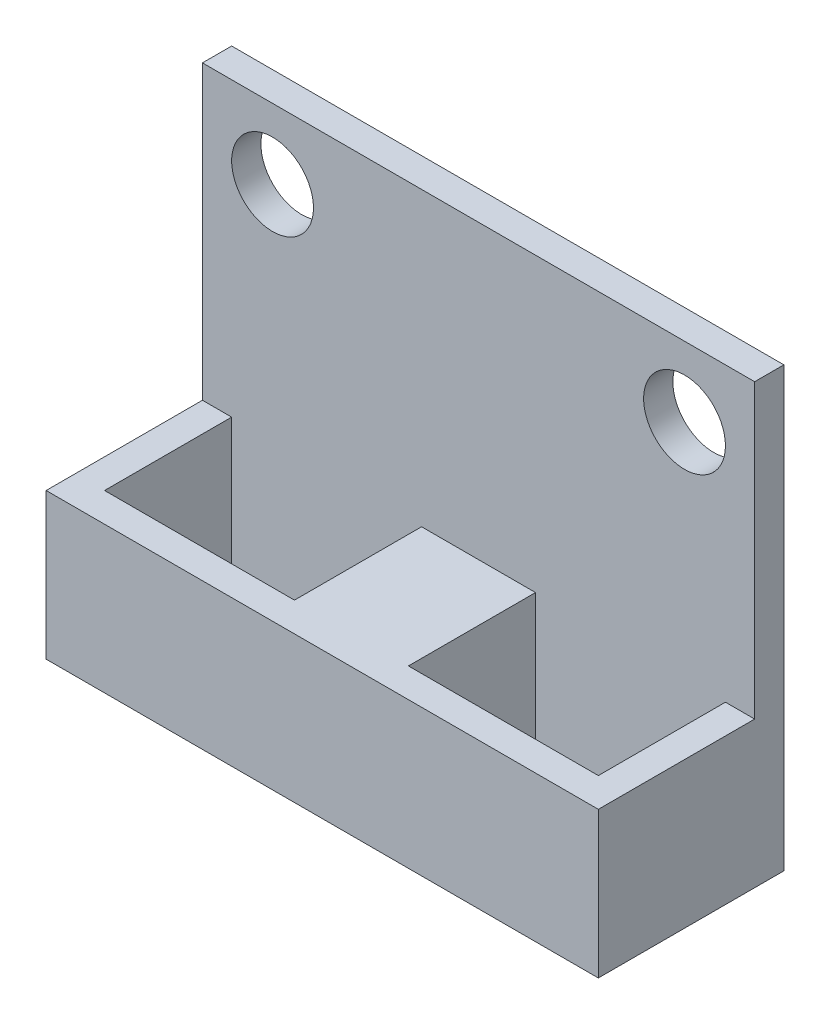
SolidWorks part; units mm, degrees
ref_plane "Front Plane" through (0, 0, 0) normal (0, 0, 1) x (1, 0, 0)
ref_plane "Top Plane" through (0, 0, 0) normal (0, 1, 0) x (1, 0, 0)
ref_plane "Right Plane" through (0, 0, 0) normal (1, 0, 0) x (0, 0, -1)
sketch "Sketch1" plane through (0, 0, 0) normal (0, 1, 0) x (1, 0, 0)
  line L1 (-9.45, -3.175) -> (9.45, -3.175)
  line L2 (-9.45, -3.175) -> (-9.45, 3.175)
  line L3 (-9.45, 3.175) -> (9.45, 3.175)
  line L4 (9.45, -3.175) -> (9.45, 3.175)
  line L5 (-9.45, -3.175) -> (9.45, 3.175) construction
  line L6 (-9.45, 3.175) -> (9.45, -3.175) construction
  line L7 (-8.45, -2.175) -> (-1.95, -2.175)
  line L8 (-8.45, -2.175) -> (-8.45, 2.175)
  line L9 (-8.45, 2.175) -> (-1.95, 2.175)
  line L10 (-1.95, -2.175) -> (-1.95, 2.175)
  line L11 (-8.45, -2.175) -> (-1.95, 2.175) construction
  line L12 (-8.45, 2.175) -> (-1.95, -2.175) construction
  line L13 (1.95, 2.175) -> (8.45, 2.175)
  line L14 (1.95, 2.175) -> (1.95, -2.175)
  line L15 (1.95, -2.175) -> (8.45, -2.175)
  line L16 (8.45, 2.175) -> (8.45, -2.175)
  line L17 (1.95, 2.175) -> (8.45, -2.175) construction
  line L18 (1.95, -2.175) -> (8.45, 2.175) construction
  point P0 (0, 0)
  point P6 (-5.2, 0)
  point P11 (5.2, 0)
  dimension "D1" = 18.9
  dimension "D2" = 6.35
  dimension "D3" = 4.35
  dimension "D4" = 6.5
  dimension "D5" = 6.5
  dimension "D6" = 4.35
  dimension "D7" = 16.9
  dimension "D8" = 8.45
extrude "Boss-Extrude1" add sketch "Sketch1" along normal blind 5
sketch "Sketch2" plane through (0, 5, 0) normal (0, 1, 0) x (1, 0, 0)
  line L0 (9.45, -3.175) -> (9.45, 3.175) construction
  line L1 (-9.45, 3.175) -> (9.45, 3.175)
  line L2 (-9.45, 3.175) -> (-9.45, 2.175)
  line L3 (-9.45, 2.175) -> (9.45, 2.175)
  line L4 (9.45, 3.175) -> (9.45, 2.175)
  dimension "D1" = 1
extrude "Boss-Extrude2" add sketch "Sketch2" along normal blind 10
sketch "Sketch3" plane through (0, 0, -2.175) normal (0, 0, 1) x (1, 0, 0)
  line L0 (9.45, 15) -> (9.45, 5) construction
  line L3 (-9.45, 15) -> (9.45, 15) construction
  line L4 (-9.45, 15) -> (-9.45, 5) construction
  circle A0 centre (7.05, 12.6) radius 1.4
  circle A1 centre (-7.05, 12.6) radius 1.4
  dimension "D1" = 2.8
  dimension "D2" = 2.8
  dimension "D3" = 2.4
  dimension "D4" = 2.4
  dimension "D5" = 2.4
  dimension "D6" = 2.4
extrude "Cut-Extrude1" cut sketch "Sketch3" against normal through all
